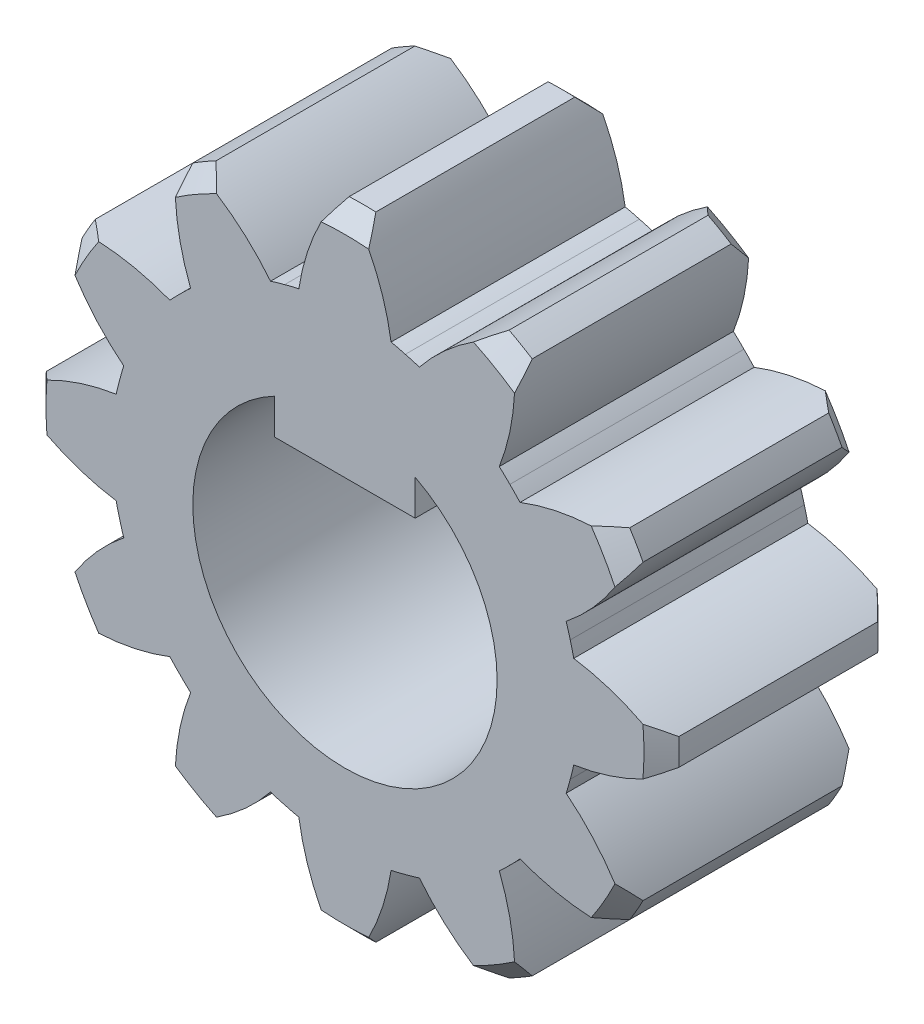
SolidWorks part; units mm, degrees
ref_plane "Front Plane" through (0, 0, 0) normal (0, 0, 1) x (1, 0, 0)
ref_plane "Top Plane" through (0, 0, 0) normal (0, 1, 0) x (1, 0, 0)
ref_plane "Right Plane" through (0, 0, 0) normal (1, 0, 0) x (0, 0, -1)
sketch "Sketch1" plane through (0, 0, 0) normal (0, 0, 1) x (1, 0, 0)
  line L0 (0, 35.0966) -> (0, -37.1453) construction
  line L1 (-45.7855, 0) -> (48.1573, 0) construction
  line L2 (-0.57, 31.4966) -> (-0.57, -32.7483) construction
  line L3 (-2.07, 30.4447) -> (-2.07, -32.7483) construction
  line L4 (-1.57, 30.4447) -> (-1.57, -32.7483) construction
  circle A0 centre (0, 0) radius 9.5
  circle A1 centre (0, 0) radius 12
  circle A2 centre (0, 0) radius 14
  arc A3 (-2.07, 9.2717) -> (-0.57, 13.9884) centre (7.6252, 8.7853) cw
  arc A4 (2.07, 9.2717) -> (0.57, 13.9884) centre (-7.6252, 8.7853) ccw
  point P15 (-2.07, 9.2717)
  point P16 (-0.57, 13.9884)
  point P17 (-1.57, 11.8969)
  dimension "D1" = 19
  dimension "D2" = 24
  dimension "D3" = 28
  dimension "D4" = 1.57
  dimension "D5" = 1
  dimension "D6" = 0.5
extrude "Boss-Extrude1" add sketch "Sketch1" along normal blind 10 contours A0 | A0 A4 A1 A3 | A1 A4 A2 A3
chamfer "Chamfer1" distance 0.75 angle 45 2 edges at (0, 14, 0) (0, 14, 10)
pattern_circular "CirPattern1" count 12 over 360 about axis through (0, 0.4791, 0) along (0, 0, 1) of "Boss-Extrude1", "Chamfer1"
ref_plane "Plane1" through (0, 0, 5) normal (0, 0, 1) x (1, 0, 0)
sketch "Sketch3" plane through (0, 0, 10) normal (0, 0, 1) x (1, 0, 0)
  line L0 (0, 0) -> (0, 35.2065) construction
  line L1 (-3, 8.75) -> (3, 8.75)
  line L2 (-3, 8.75) -> (-3, 4.25)
  line L3 (-3, 4.25) -> (3, 4.25)
  line L4 (3, 8.75) -> (3, 4.25)
  line L5 (-29.4786, 6.5) -> (57.0056, 6.5) construction
  circle A0 centre (0, 0) radius 6.5
  dimension "D1" = 13
  dimension "D2" = 6
  dimension "D3" = 4.5
extrude "Cut-Extrude2" cut sketch "Sketch3" against normal blind 10 contours L2 A0 L4 L3
